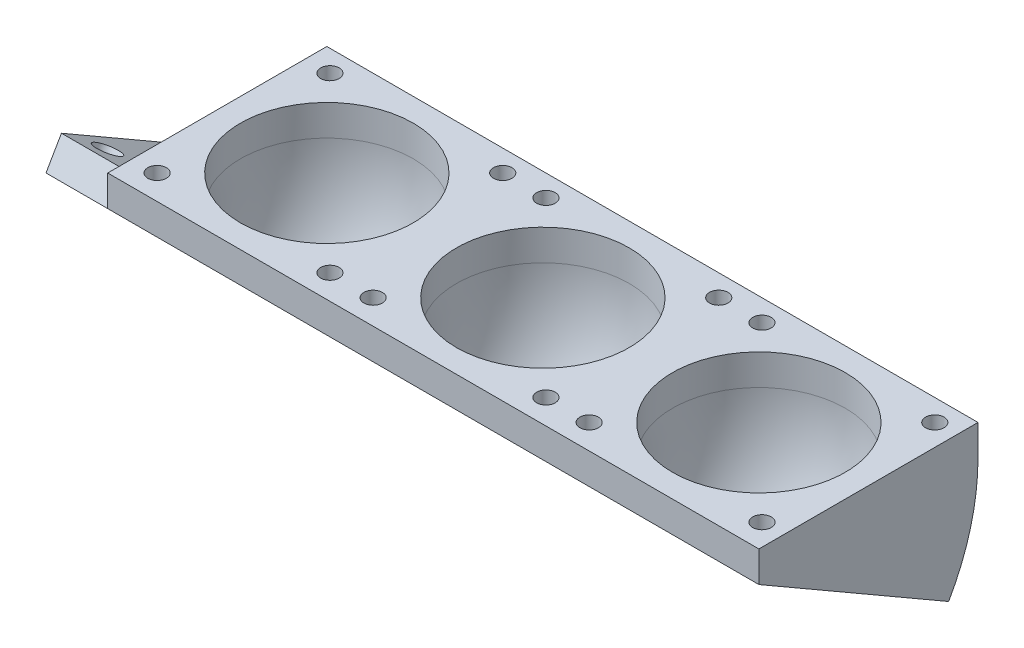
SolidWorks part; units mm, degrees
ref_plane "Front Plane" through (0, 0, 0) normal (0, 0, 1) x (1, 0, 0)
ref_plane "Top Plane" through (0, 0, 0) normal (0, 1, 0) x (1, 0, 0)
ref_plane "Right Plane" through (0, 0, 0) normal (1, 0, 0) x (0, 0, -1)
sketch "Sketch1" plane through (0, 0, 0) normal (0, 1, 0) x (1, 0, 0)
  line L0 (-15.9922, 44.0544) -> (-15.9922, 65.6687) construction
  line L1 (-51.4922, 44.0544) -> (19.5078, 44.0544)
  line L2 (-51.4922, 44.0544) -> (-51.4922, -26.9456)
  line L3 (-51.4922, -26.9456) -> (19.5078, -26.9456)
  line L4 (19.5078, 44.0544) -> (19.5078, -26.9456)
  line L5 (19.5078, 8.5544) -> (42.4205, 8.5544) construction
  circle A0 centre (-43.4922, 37.0544) radius 3
  circle A1 centre (12.5078, 37.0544) radius 3
  circle A2 centre (12.5078, -18.9456) radius 3
  circle A3 centre (-43.4922, -18.9456) radius 3
  circle A4 centre (-15.9922, 8.5544) radius 28
  point P16 (0, 0)
  point P17 (0, 0)
  dimension "D7" = 6
  dimension "D8" = 6
  dimension "D9" = 6
  dimension "D10" = 6
  dimension "D13" = 56
  dimension "D1" = 71
  dimension "D2" = 71
  dimension "D3" = 56
  dimension "D4" = 56
  dimension "D5" = 56
  dimension "D6" = 56
  dimension "D11" = 7
  dimension "D12" = 7
extrude "Boss-Extrude1" add sketch "Sketch1" along normal blind 10
sketch "Sketch2" plane through (0, 0, 0) normal (0, -1, 0) x (1, 0, 0)
  line L4 (-51.4922, 26.9456) -> (-51.4922, -44.0544)
  line L5 (-51.4922, -44.0544) -> (19.5078, -44.0544)
  line L6 (19.5078, -44.0544) -> (19.5078, 26.9456)
  line L7 (19.5078, 26.9456) -> (-51.4922, 26.9456)
  line L8 (-51.4922, 26.9456) -> (-51.4922, -44.0544)
  line L9 (-51.4922, -44.0544) -> (19.5078, -44.0544)
  line L10 (19.5078, -44.0544) -> (19.5078, 26.9456)
  line L11 (19.5078, 26.9456) -> (-51.4922, 26.9456)
  circle A0 centre (-15.9922, -8.5544) radius 28 construction
  circle A1 centre (-15.9922, -8.5544) radius 28
  dimension "D1" = 0
revolve "Revolve1" add sketch "Sketch2" angle 30 about L11
pattern_linear "LPattern1" count 3 spacing 70 along (1, 0, 0) of "Boss-Extrude1", "Revolve1"
sketch "Sketch3" plane through (0, -11.6678, 6.7364) normal (0, -0.866, 0.5) x (1, 0, 0)
  line L1 (-51.4922, 23.3356) -> (-71.4922, 23.3356)
  line L2 (-51.4922, 23.3356) -> (-51.4922, -47.6644)
  line L3 (-51.4922, -47.6644) -> (-71.4922, -47.6644)
  line L4 (-71.4922, 23.3356) -> (-71.4922, -47.6644)
  point P10 (0, 0)
  point P12 (0, 0)
  dimension "D2" = 20
extrude "Boss-Extrude2" add sketch "Sketch3" against normal blind 10
sketch "Sketch4" plane through (0, -11.6678, 6.7364) normal (0, -0.866, 0.5) x (1, 0, 0)
  line L0 (-71.4922, 23.3356) -> (-71.4922, -47.6644) construction
  line L1 (-51.4922, 23.3356) -> (-71.4922, 23.3356) construction
  line L2 (-71.4922, -47.6644) -> (-51.4922, -47.6644) construction
  circle A0 centre (-63.4922, 15.3356) radius 4
  circle A1 centre (-63.4922, -39.6644) radius 4
  dimension "D1" = 8
  dimension "D2" = 8
  dimension "D5" = 8
  dimension "D6" = 8
  dimension "D7" = 8
  dimension "D8" = 8
extrude "Cut-Extrude1" cut sketch "Sketch4" against normal blind 10
